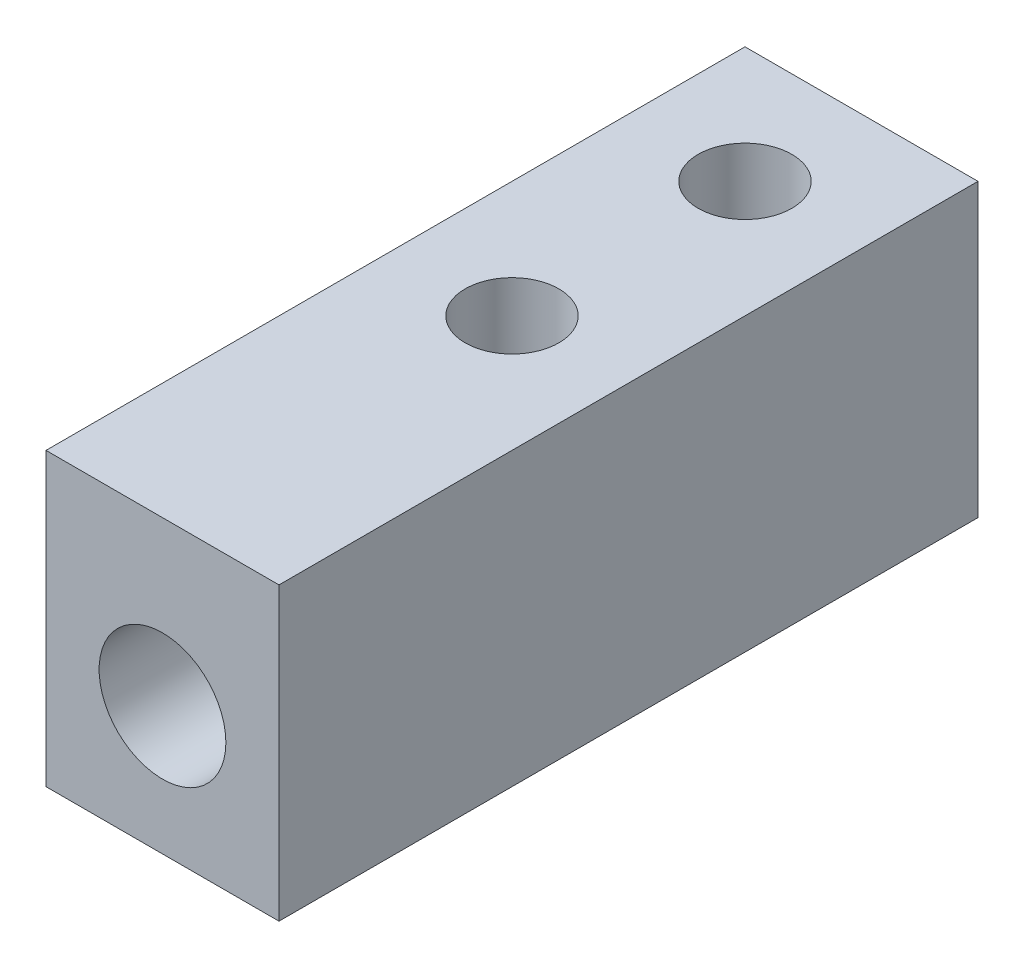
SolidWorks part; units mm, degrees
material "6061-T6 (SS)"
ref_plane "Front Plane" through (0, 0, 0) normal (0, 0, 1) x (1, 0, 0)
ref_plane "Top Plane" through (0, 0, 0) normal (0, 1, 0) x (1, 0, 0)
ref_plane "Right Plane" through (0, 0, 0) normal (1, 0, 0) x (0, 0, -1)
sketch "Sketch1" plane through (0, 0, 0) normal (0, 0, 1) x (1, 0, 0)
  line L1 (-6.35, -6.35) -> (6.35, -6.35)
  line L2 (-6.35, -6.35) -> (-6.35, 6.35)
  line L3 (-6.35, 6.35) -> (6.35, 6.35)
  line L4 (6.35, -6.35) -> (6.35, 6.35)
  line L5 (-6.35, -6.35) -> (6.35, 6.35) construction
  line L6 (-6.35, 6.35) -> (6.35, -6.35) construction
  point P0 (0, 0)
  dimension "D1" = 12.7
  dimension "D2" = 12.7
extrude "Boss-Extrude1" add sketch "Sketch1" along normal mid plane 31.75
hole_wizard "#7 (0.201) Diameter Hole1" positions "Sketch2" profile "Sketch4" hole size "#7" standard "ANSI Inch" end condition through all
sketch "Sketch2" plane through (0, 6.35, 0) normal (0, 1, 0) x (1, 0, 0)
  line L0 (-7.9073, 0) -> (11.9756, 0) construction
  line L1 (6.35, 15.875) -> (-6.35, 15.875) construction
  point P8 (0, 9.525)
  point P13 (0, -3.175)
  dimension "D1" = 6.35
  dimension "D2" = 12.7
sketch "Sketch4" plane through (0, 6.35, 3.175) normal (1, 0, 0) x (0, 0, 1)
  line L0 (0, 0) -> (0, 12.7)
  line L1 (0, 12.7) -> (2.5527, 12.7)
  line L2 (2.5527, 12.7) -> (2.5527, 0)
  line L5 (2.5527, 0) -> (0, 0)
  line L11 (0, -6.35) -> (0, 107.95) construction
  dimension "Thru Hole Dia." = 5.1054
  dimension "Thru Hole Depth" = 12.7
sketch "Sketch5" plane through (0, 0, 15.875) normal (0, 0, 1) x (1, 0, 0)
  line L0 (-6.35, -6.35) -> (6.35, -6.35) construction
  line L1 (6.35, -6.35) -> (6.35, 6.35) construction
  line L2 (6.35, 6.35) -> (-6.35, 6.35) construction
  line L3 (-6.35, 6.35) -> (-6.35, -6.35) construction
  line L4 (-6.35, -6.35) -> (6.35, -6.35)
  line L5 (6.35, -6.35) -> (6.35, 6.35)
  line L6 (6.35, 6.35) -> (-6.35, 6.35)
  line L7 (-6.35, 6.35) -> (-6.35, -6.35)
extrude "Boss-Extrude2" add sketch "Sketch5" along normal blind 6.35
hole_wizard "5/16-24 Tapped Hole1" positions "Sketch6" profile "Sketch7" tap size "5/16-24" standard "ANSI Inch"
sketch "Sketch6" plane through (0, 0, 22.225) normal (0, 0, 1) x (1, 0, 0)
  point P0 (0, -2.54)
  dimension "D1" = 2.54
cosmetic thread "Hole Thread1" parameters "D1"=16.002, "D2"=7.9375
sketch "Sketch7" plane through (0, -2.54, 22.225) normal (1, 0, 0) x (0, -1, 0)
  line L0 (0, 0) -> (0, 21.3796)
  line L1 (0, 21.3796) -> (3.4544, 19.304)
  line L2 (3.4544, 19.304) -> (3.4544, 0)
  line L5 (3.4544, 0) -> (0, 0)
  line L10 (0, 21.3796) -> (-3.4544, 19.304) construction
  line L11 (0, -6.35) -> (0, 107.95) construction
  dimension "Tap Drill Dia." = 6.9088
  dimension "Tap Drill Depth" = 19.304
  dimension "Drill Angle" = 118
sketch "Sketch9" plane through (0, -6.35, 0) normal (0, -1, 0) x (1, 0, 0)
  circle A1 centre (0, 3.175) radius 2.5527
  circle A2 centre (0, 3.175) radius 2.5527
  circle A3 centre (0, -9.525) radius 2.5527
  circle A4 centre (0, -9.525) radius 2.5527
  circle M3 centre (0, -9.525) radius 2.5527
  circle M4 centre (0, 3.175) radius 2.5527
  line M5 (-6.35, -15.875) -> (6.35, -15.875)
  line M6 (6.35, -15.875) -> (6.35, 22.225)
  line M7 (6.35, 22.225) -> (-6.35, 22.225)
  line M8 (-6.35, 22.225) -> (-6.35, -15.875)
  dimension "D1" = 0
  dimension "D2" = 0
extrude "Boss-Extrude4" add sketch "Sketch9" along normal blind 3.175 contours M8 M5 M6 M7 M4 M3
